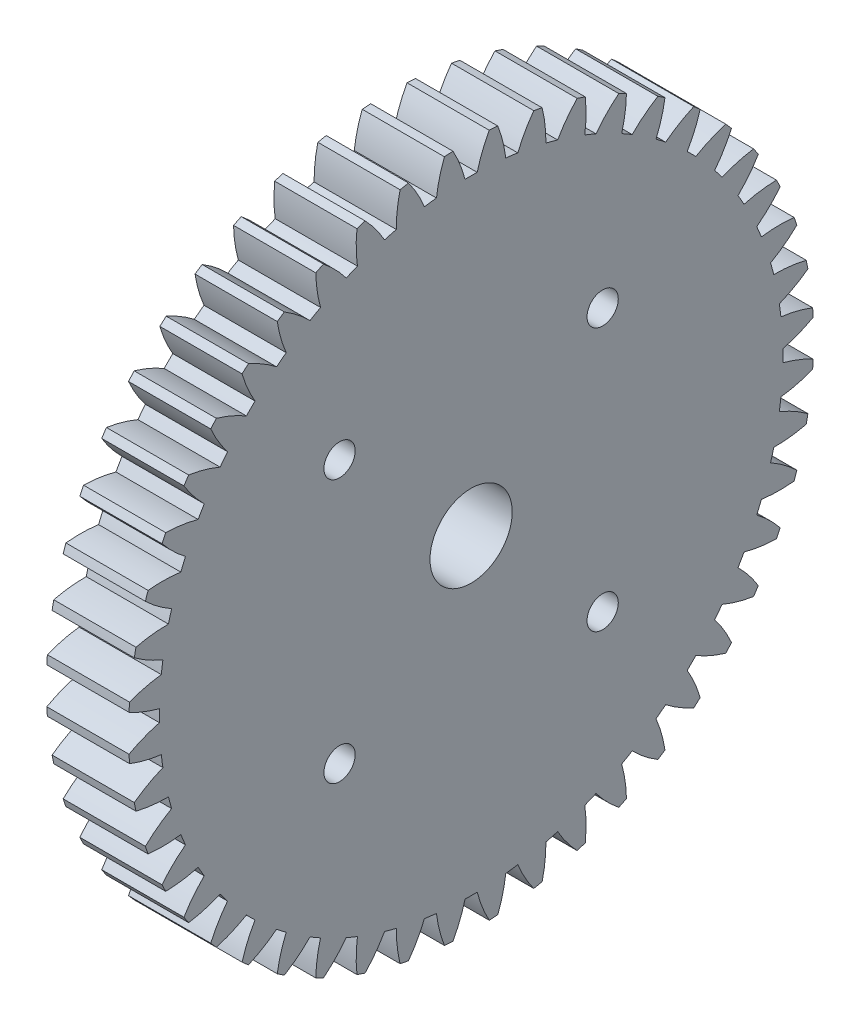
SolidWorks part; units mm, degrees
ref_plane "Plane1" through (0, 0, 0) normal (0, 0, 1) x (1, 0, 0)
ref_plane "Plane2" through (0, 0, 0) normal (0, 1, 0) x (1, 0, 0)
ref_plane "Plane3" through (0, 0, 0) normal (1, 0, 0) x (0, 0, -1)
sketch "HoldingSke" plane through (0, 0, 0) normal (0, 1, 0) x (1, 0, 0)
  line L0 (0, 0) -> (203.951, -226.5105)
  line L1 (-15, 0) -> (100, 0) construction
  line L2 (0, 0) -> (-2.1039, 2.3779)
  line L3 (0, 0) -> (-11.863, 4.5341)
  line L4 (0, 0) -> (5.7786, 6.4178)
  line L5 (0, 0) -> (-47.5972, -17.7524)
  line L6 (0, 0) -> (-10.5278, -7.1032)
  line L7 (-2.1039, 2.3779) -> (8.8308, 51.9871)
  line L8 (-76.2, 54.61) -> (-61.976, 54.61)
  line L9 (-71.009, 38.7566) -> (-53.1078, 45.2721)
  line L10 (-76.2, 71.12) -> (104.1128, 71.12)
  line L11 (0, 0) -> (-12.7, 0)
  line L12 (-76.2, 101.6) -> (-76.1147, 101.6)
  line L13 (24.9733, 27.94) -> (52.9518, 28.4284)
  line L14 (24.9733, 27.94) -> (24.9746, 27.94)
  line L15 (24.9733, 27.94) -> (100.4006, 29.5858)
  circle A0 centre (0, 0) radius 6.35
  circle A1 centre (0, 0) radius 38.1
  circle A2 centre (0, 0) radius 38.1
  circle A3 centre (0, 0) radius 6.35
  dimension "MHD" = 76.2
  dimension "Hub_dia" = 76.2
  dimension "Bore" = 12.7
  dimension "MBD" = 12.7
  dimension "Num_teeth" = 48
  dimension "Pitch" = 304.8
  dimension "Overall_len" = 50.8
  dimension "Show_teeth" = 48
  dimension "Thickness" = 12.7
  dimension "OAL" = 50.8001
  dimension "T_dim" = 14.224
  dimension "Ap" = 20
  dimension "H" = 19.05
  dimension "Pitch_radius" = 180.3128
  dimension "Width" = 12.7
  dimension "Backlash" = 0.0853
  dimension "Addendum_fac" = 1
  dimension "Dedendum_fac" = 1.25
  dimension "Clearance_fac" = 0.25
  dimension "Dedendum_add" = 0.0013
sketch "BasProSke" plane through (0, 0, 0) normal (0, 1, 0) x (1, 0, 0)
  line L0 (-10, 0) -> (60, 0) construction
  line L1 (0, 0) -> (0, 52.9167)
  line L2 (0, 0) -> (12.7, 0)
  line L3 (12.7, 0) -> (12.7, 52.9167)
  line L4 (12.7, 52.9167) -> (0, 52.9167)
  dimension "Thickness" = 12.7
  dimension "Diameter" = 105.8333
revolve "Base-Revolve" add sketch "BasProSke" angle 360 about L0
sketch "TooCutSke" plane through (0, 0, 0) normal (1, 0, 0) x (0, 0, -1)
  line L1 (0, 0) -> (0, 107) construction
  line L2 (0, 0) -> (-1.8115, 50.7677) construction
  line L3 (0, 0) -> (-6.642, 101.3375) construction
  line L4 (-1.8115, 50.7677) -> (-3.321, 50.6688) construction
  arc A0 (0.9387, 48.1437) -> (-0.9387, 48.1437) centre (0, 0) ccw
  arc A1 (2.8166, 52.8671) -> (-2.8166, 52.8671) centre (0, 0) ccw
  circle A2 centre (0, 0) radius 50.8 construction
  circle A3 centre (0, 0) radius 47.7364 construction
  arc A4 (-0.9387, 48.1437) -> (-2.8166, 52.8671) centre (-20.6117, 43.0572) ccw
  arc A5 (2.8166, 52.8671) -> (0.9387, 48.1437) centre (20.6117, 43.0572) ccw
  dimension "Root_dia" = 96.3058
  dimension "Overcut_dia" = 105.8841
  dimension "Pitch_dia" = 101.6
  dimension "Base_dia" = 95.4728
  dimension "Flank_rad" = 20.32
  dimension "Half_ang" = 3.75
  dimension "Half_CT" = 1.5128
extrude "ToothCut" cut sketch "TooCutSke" along normal through all
fillet "Breaks" [suppressed] radius 0.0423
fillet "RootFillets" [suppressed] radius 0.5304
pattern_circular "TeethCuts" count 48 every 7.5 about axis through (-10, 0, 0) along (1, 0, 0) of "ToothCut", "RootFillets", "Breaks"
sketch "HubNeaOneSke" plane through (0, 0, 0) normal (-1, 0, 0) x (0, 0, 1)
  circle A0 centre (0, 0) radius 38.1
  dimension "Diameter" = 76.2
extrude "HubNearOne" [suppressed] add sketch "HubNeaOneSke" along normal blind 38.1001
sketch "HubNeaBotSke" plane through (0, 0, 0) normal (-1, 0, 0) x (0, 0, 1)
  circle A0 centre (0, 0) radius 38.1
  dimension "Diameter" = 76.2
extrude "HubNearBoth" [suppressed] add sketch "HubNeaBotSke" along normal blind 19.05
ref_plane "FarPln" through (12.7, 0, 0) normal (1, 0, 0) x (0, 0, -1)
sketch "HubFarSke" plane through (12.7, 0, 0) normal (1, 0, 0) x (0, 0, -1)
  circle A0 centre (0, 0) radius 38.1
  dimension "Diameter" = 76.2
extrude "HubFar" [suppressed] add sketch "HubFarSke" along normal blind 19.05
sketch "BorSke" plane through (0, 0, 0) normal (1, 0, 0) x (0, 0, -1)
  circle A0 centre (0, 0) radius 6.35
  dimension "Diameter" = 12.7
extrude "Bore" cut sketch "BorSke" along normal mid plane 101.6001
sketch "KeySke" plane through (0, 0, 0) normal (1, 0, 0) x (0, 0, -1)
  line L0 (-1.5875, 0) -> (-1.5875, 7.874)
  line L1 (-1.5875, 7.874) -> (1.5875, 7.874)
  line L2 (1.5875, 7.874) -> (1.5875, 0)
  line L3 (0, 0) -> (0, 34) construction
  line L4 (-1.5875, 0) -> (1.5875, 0)
  dimension "Offset" = 7.874
  dimension "Width" = 3.175
extrude "Keyway" [suppressed] cut sketch "KeySke" along normal mid plane 101.6001
pattern_circular "Keyway2" [suppressed] count 2 every 90 about axis through (-10, 0, 0) along (1, 0, 0)
sketch "Sketch2" plane through (12.7, 0, 0) normal (1, 0, 0) x (0, 0, -1)
  line L0 (-41.1163, 0) -> (39.0228, 0) construction
  line L1 (0, 22.178) -> (0, -28.0145) construction
  line L2 (-20.32, 20.32) -> (20.32, 20.32) construction
  line L3 (20.32, 20.32) -> (20.32, -20.32) construction
  circle A0 centre (-20.32, 20.32) radius 2.413
  circle A1 centre (-20.32, -20.32) radius 2.413
  circle A2 centre (20.32, -20.32) radius 2.413
  circle A3 centre (20.32, 20.32) radius 2.413
  point P10 (20.32, 0)
  point P11 (0, 20.32)
  dimension "D1" = 4.826
  dimension "D2" = 40.64
  dimension "D3" = 40.64
extrude "Cut-Extrude1" cut sketch "Sketch2" against normal up to surface (12.7 mm away) up to face at (0, 0, -6.35)
equation "' \"Pitch@HoldingSke\" = 4"
equation "' \"Num_teeth@HoldingSke\" = 12"
equation "' \"Ap@HoldingSke\" =  20"
equation "' \"Ap@HoldingSke\" = 20"
equation "' \"Width@HoldingSke\" = 0.5"
equation "' \"Hub_dia@HoldingSke\"= 1"
equation "' \"Hub_dia@HoldingSke\" = 1"
equation "' \"Overall_len@HoldingSke\" = 1.0"
equation "' \"Bore@HoldingSke\" = 0.75"
equation "' \"T_dim@HoldingSke\" = 0.85"
equation "' \"Width@KeySke\" = 0.25"
equation "' \"Show_teeth@HoldingSke\" = 13"
equation "' \"Backlash@HoldingSke\" = 0.009"
equation "' \"Addendum_fac@HoldingSke\" = 1.0"
equation "' \"Dedendum_fac@HoldingSke\" = 1.25"
equation "' \"Dedendum_add@HoldingSke\" = 0.00005"
equation "' \"Clearance_fac@HoldingSke\" = 0.25"
equation "' \"Pitch@HoldingSke\" = 0.5"
equation "' \"Num_teeth@HoldingSke\" = 23"
equation "' \"Show_teeth@HoldingSke\" = 23"
equation "' \"Backlash@HoldingSke\" = 0.0375"
equation "\"Overcut_dia@TooCutSke\" = (\"Num_teeth@HoldingSke\" + 2 * \"Addendum_fac@HoldingSke\") / \"Pitch@HoldingSke\" + 0.002"
equation "\"Pitch_dia@TooCutSke\" = \"Num_teeth@HoldingSke\" / \"Pitch@HoldingSke\""
equation "\"Base_dia@TooCutSke\" = \"Num_teeth@HoldingSke\" / \"Pitch@HoldingSke\" * cos((\"Ap@HoldingSke\"  * 3.14159265 / 180))"
equation "\"Root_dia@TooCutSke\" = (\"Num_teeth@HoldingSke\" + 2) / \"Pitch@HoldingSke\" - 2 * (\"Addendum_fac@HoldingSke\" + \"Dedendum_fac@HoldingSke\") / \"Pitch@HoldingSke\" - \"Dedendum_add@HoldingSke\" * 2"
equation "\"Half_ang@TooCutSke\" = 180 / \"Num_teeth@HoldingSke\""
equation "\"Half_CT@TooCutSke\" = \"Num_teeth@HoldingSke\" / \"Pitch@HoldingSke\" * sin((3.14159265 / 2 / \"Num_teeth@HoldingSke\")) / 2 - 7 * \"Backlash@HoldingSke\" / 4"
equation "\"Flank_rad@TooCutSke\" = \"Num_teeth@HoldingSke\" / \"Pitch@HoldingSke\" / 5"
equation "\"Radius@RootFillets\" = \"Clearance_fac@HoldingSke\" / \"Pitch@HoldingSke\" + \"Dedendum_add@HoldingSke\""
equation "\"Break_rad@Breaks\" = 0.02 / \"Pitch@HoldingSke\""
equation "\"Thickness@HoldingSke\" = \"Width@HoldingSke\""
equation "\"OAL@HoldingSke\" = \"Thickness@HoldingSke\""
equation "\"MHD@HoldingSke\" = (\"Num_teeth@HoldingSke\" + 2) / \"Pitch@HoldingSke\" - 2 * (\"Addendum_fac@HoldingSke\" + \"Dedendum_fac@HoldingSke\")  / \"Pitch@HoldingSke\" - \"Dedendum_add@HoldingSke\" * 2"
equation "\"MBD@HoldingSke\" = (\"Num_teeth@HoldingSke\" + 2) / \"Pitch@HoldingSke\" - 2 * (\"Addendum_fac@HoldingSke\" + \"Dedendum_fac@HoldingSke\")  / \"Pitch@HoldingSke\" - \"Dedendum_add@HoldingSke\" * 2 - 0.002"
equation "\"MHD@HoldingSke\" = ((sgn( \"MHD@HoldingSke\" - \"Hub_dia@HoldingSke\" )-1)*( \"MHD@HoldingSke\" - \"Hub_dia@HoldingSke\" ))/-2+ \"Hub_dia@HoldingSke\""
equation "\"MBD@HoldingSke\" = ((sgn( \"MBD@HoldingSke\" - \"Bore@HoldingSke\" )-1)*( \"MBD@HoldingSke\" - \"Bore@HoldingSke\" ))/-2+ \"Bore@HoldingSke\""
equation "\"OAL@HoldingSke\" = ((sgn( \"OAL@HoldingSke\" - \"Overall_len@HoldingSke\" )+1)*( \"OAL@HoldingSke\" - \"Overall_len@HoldingSke\" ))/2 + \"Overall_len@HoldingSke\" + 0.000002"
equation "\"Num_teeth@TeethCuts\" = int( \"Show_teeth@HoldingSke\" ) + 1"
equation "\"Num_teeth@TeethCuts\" = ((sgn( \"Num_teeth@TeethCuts\" - \"Num_teeth@HoldingSke\" )-1)*( \"Num_teeth@TeethCuts\" - \"Num_teeth@HoldingSke\" ))/-2+ \"Num_teeth@HoldingSke\""
equation "\"Num_teeth@TeethCuts\" = ((sgn( \"Num_teeth@TeethCuts\" - 2.0)+1)*( \"Num_teeth@TeethCuts\" - 2.0))/2 +2.0"
equation "\"Angle@TeethCuts\" = 360.0 / \"Num_teeth@HoldingSke\""
equation "\"Diameter@BasProSke\" = (\"Num_teeth@HoldingSke\" + 2 * \"Addendum_fac@HoldingSke\") / \"Pitch@HoldingSke\""
equation "\"Thickness@BasProSke\"  = \"Thickness@HoldingSke\""
equation "' \"Fillet_rad@BasProSke\" =  \"Thickness@HoldingSke\" * 0.05"
equation "' \"Fillet_rad@BasProSke\" = \"Thickness@HoldingSke\" * 0.05"
equation "\"MHD@HoldingSke\" = ((sgn( \"MHD@HoldingSke\" - \"Root_dia@TooCutSke\" )-1)*( \"MHD@HoldingSke\" - \"Root_dia@TooCutSke\" ))/-2+ \"Root_dia@TooCutSke\""
equation "\"Diameter@HubNeaOneSke\" = \"MHD@HoldingSke\""
equation "\"Length@HubNearOne\" = \"OAL@HoldingSke\" - \"Thickness@BasProSke\""
equation "\"Diameter@HubNeaBotSke\" = \"MHD@HoldingSke\""
equation "\"Length@HubNearBoth\" = ( \"OAL@HoldingSke\" - \"Thickness@BasProSke\" ) / 2.0"
equation "\"Thickness@FarPln\" = \"Thickness@BasProSke\""
equation "\"Diameter@HubFarSke\" = \"MHD@HoldingSke\""
equation "\"Length@HubFar\" = ( \"OAL@HoldingSke\" - \"Thickness@BasProSke\" ) / 2.0"
equation "\"Diameter@BorSke\" = \"MBD@HoldingSke\""
equation "\"D1@Bore\" = \"OAL@HoldingSke\" * 2.0"
equation "\"D1@Keyway\" = \"OAL@HoldingSke\" * 2.0"
equation "\"Offset@KeySke\" = \"T_dim@HoldingSke\" - \"MBD@HoldingSke\" / 2.0"
